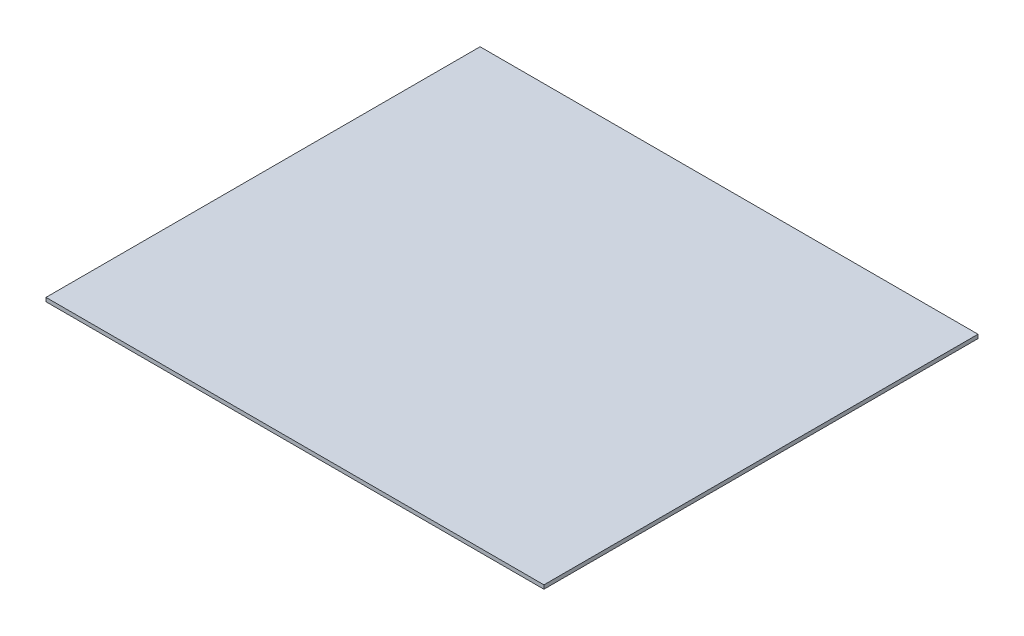
SolidWorks part; units mm, degrees
ref_plane "Plan de face" through (0, 0, 0) normal (0, 0, 1) x (1, 0, 0)
ref_plane "Plan de dessus" through (0, 0, 0) normal (0, 1, 0) x (1, 0, 0)
ref_plane "Plan de droite" through (0, 0, 0) normal (1, 0, 0) x (0, 0, -1)
sketch "Esquisse1" plane through (0, 0, 0) normal (0, 1, 0) x (1, 0, 0)
  line L1 (0, 0) -> (390, 0)
  line L2 (0, 0) -> (0, -340)
  line L3 (0, -340) -> (390, -340)
  line L4 (390, 0) -> (390, -340)
  dimension "D1" = 390
  dimension "D2" = 340
extrude "Boss.-Extru.1" add sketch "Esquisse1" along normal blind 3
